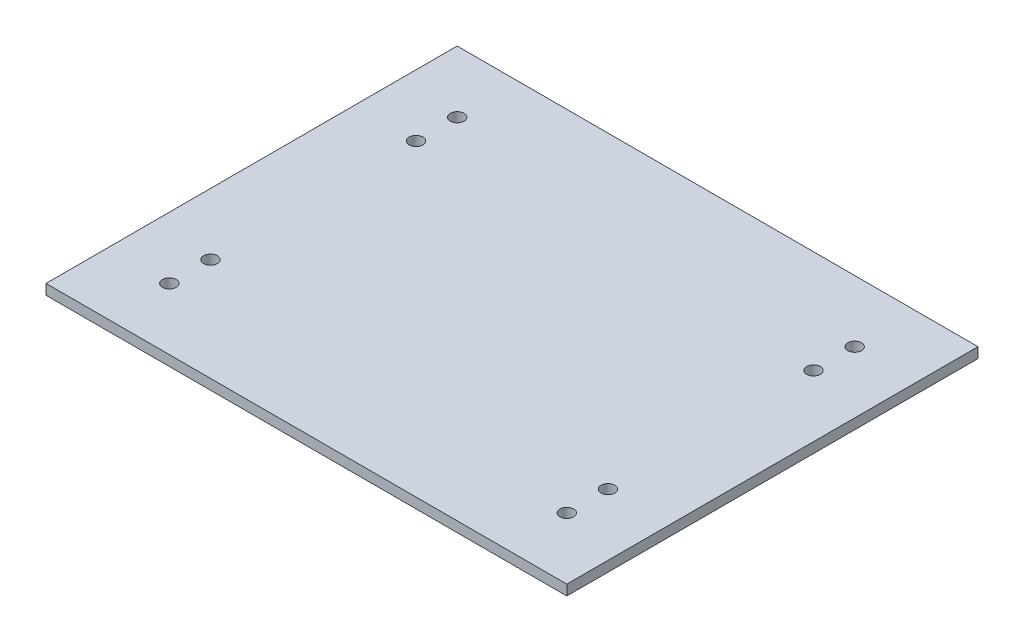
SolidWorks part; units mm, degrees
ref_plane "Front Plane" through (0, 0, 0) normal (0, 0, 1) x (1, 0, 0)
ref_plane "Top Plane" through (0, 0, 0) normal (0, 1, 0) x (1, 0, 0)
ref_plane "Right Plane" through (0, 0, 0) normal (1, 0, 0) x (0, 0, -1)
sketch "Sketch1" plane through (0, 0, 0) normal (0, 1, 0) x (1, 0, 0)
  line L1 (-47.0317, 71.8994) -> (104.9683, 71.8994)
  line L2 (-47.0317, 71.8994) -> (-47.0317, -48.1006)
  line L3 (-47.0317, -48.1006) -> (104.9683, -48.1006)
  line L4 (104.9683, 71.8994) -> (104.9683, -48.1006)
  dimension "D1" = 120
  dimension "D2" = 152
extrude "Boss-Extrude1" add sketch "Sketch1" along normal blind 3
sketch "Sketch2" plane through (0, 3, 0) normal (0, 1, 0) x (-1, 0, 0)
  circle A1 centre (-86.9683, 30.1006) radius 2
  dimension "D1" = 4
extrude "Cut-Extrude1" cut sketch "Sketch2" against normal through all
sketch "Sketch5" plane through (0, 3, 0) normal (0, 1, 0) x (-1, 0, 0)
  circle A0 centre (-86.9683, 18.1006) radius 2
  dimension "D1" = 4
extrude "Cut-Extrude3" cut sketch "Sketch5" against normal through all
sketch "Sketch6" plane through (0, 3, 0) normal (0, 1, 0) x (-1, 0, 0)
  circle A0 centre (-86.9683, -41.8994) radius 2
  circle A1 centre (29.0317, -53.8994) radius 2
  circle A2 centre (-86.9683, -53.8994) radius 2
  circle A3 centre (29.0317, -41.8994) radius 2
  circle A4 centre (29.0317, 18.1006) radius 2
  circle A5 centre (29.0317, 30.1006) radius 2
  dimension "D1" = 4
extrude "Cut-Extrude4" cut sketch "Sketch6" against normal through all
